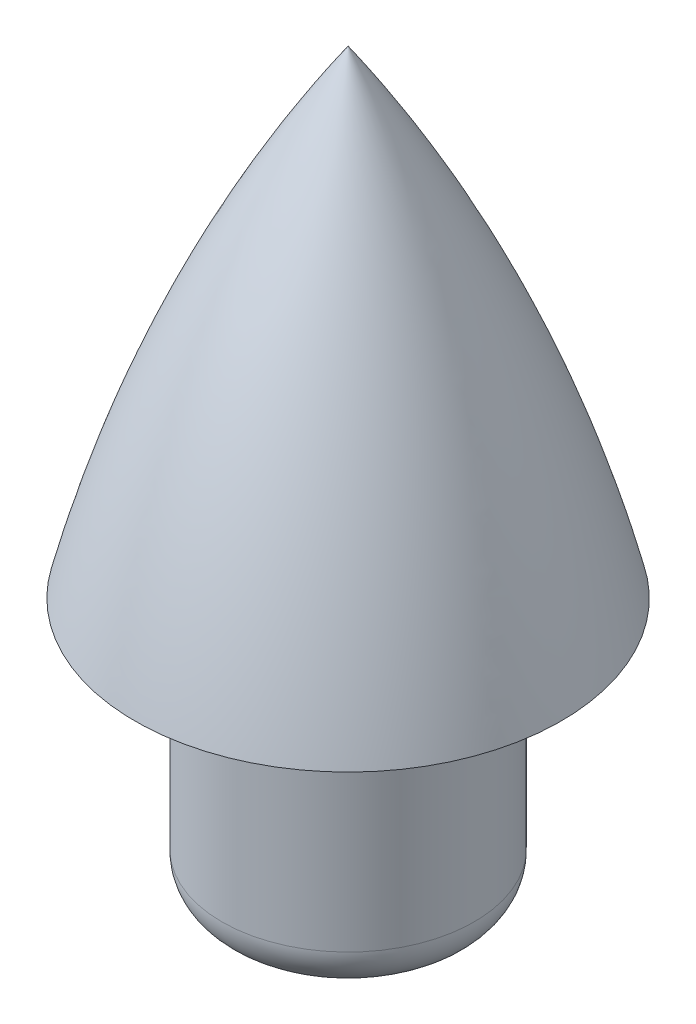
SolidWorks part; units mm, degrees
ref_plane "Plano frontal" through (0, 0, 0) normal (0, 0, 1) x (1, 0, 0)
ref_plane "Plano superior" through (0, 0, 0) normal (0, 1, 0) x (1, 0, 0)
ref_plane "Plano direito" through (0, 0, 0) normal (1, 0, 0) x (0, 0, -1)
sketch "Esboço1" plane through (0, 0, 0) normal (0, 1, 0) x (1, 0, 0)
  circle A0 centre (0, 0) radius 14.5
  dimension "D1" = 29
extrude "Ressalto-extrusão1" add sketch "Esboço1" along normal blind 30
ref_plane "Plano2" through (0, 30, 0) normal (0, 1, 0) x (1, 0, 0)
sketch "Esboço2" plane through (0, 30, 0) normal (0, 1, 0) x (1, 0, 0)
  circle A0 centre (0, 0) radius 24.5
  dimension "D1" = 49
sketch "Esboço3" plane through (0, 0, 0) normal (0, 0, 1) x (1, 0, 0)
  line L0 (0, 30) -> (0, 85)
  line L1 (24.5, 30) -> (-24.5, 30) construction
  line L3 (0, 30) -> (24.5, 30)
  arc A0 (0, 85) -> (24.5, 30) centre (-140.5853, -10.5812) cw
  dimension "D3" = 170
  dimension "D1" = 55
  dimension "D2" = 24.5
revolve "Revolução2" add sketch "Esboço3" angle 360 about L0
fillet "Filete1" radius 5 1 edges at (0, 0, 14.5)
